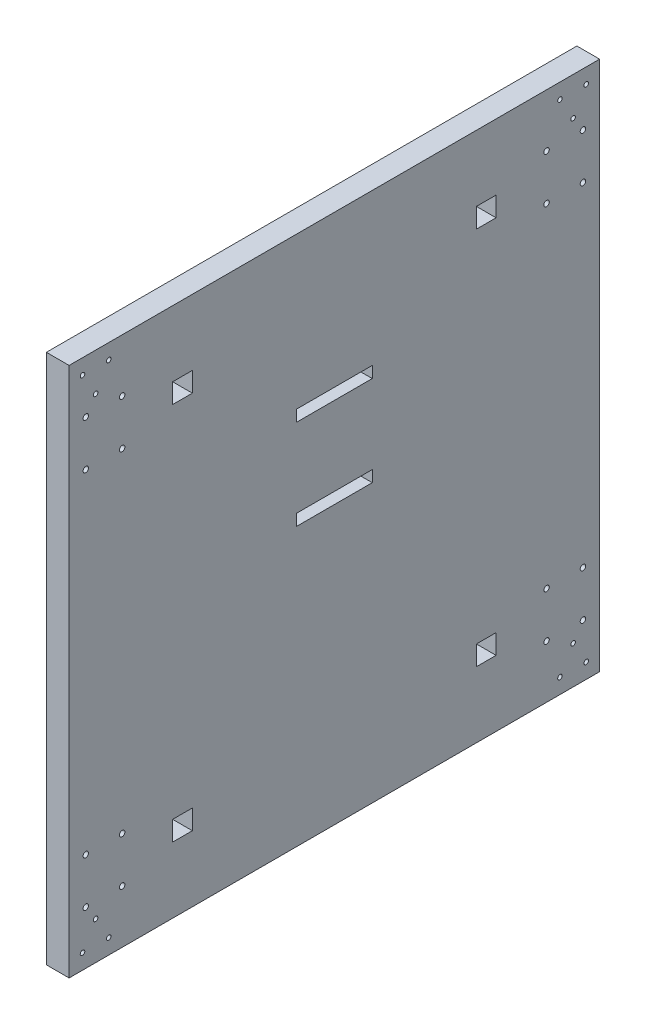
SolidWorks part; units mm, degrees
ref_plane "Front Plane" through (0, 0, 0) normal (0, 0, 1) x (1, 0, 0)
ref_plane "Top Plane" through (0, 0, 0) normal (0, 1, 0) x (1, 0, 0)
ref_plane "Right Plane" through (0, 0, 0) normal (1, 0, 0) x (0, 0, -1)
sketch "Sketch2" plane through (0, 0, 0) normal (1, 0, 0) x (0, 0, -1)
  line L0 (-336.1732, 61.8255) -> (-336.1732, -288.1745)
  line L1 (-336.1732, 61.8255) -> (13.8268, 61.8255)
  line L3 (-336.1732, -288.1745) -> (13.8268, -288.1745)
  line L4 (13.8268, 61.8255) -> (13.8268, -288.1745)
  line L10 (-161.1732, -38.1745) -> (-136.1732, -38.1745)
  line L11 (-54.4741, 18.3245) -> (-67.472, 18.3245)
  line L12 (-67.472, 5.3266) -> (-67.472, 18.3245)
  line L13 (-267.8723, 5.3266) -> (-254.8744, 5.3266)
  line L14 (-54.4741, 5.3266) -> (-67.472, 5.3266)
  line L15 (-267.8723, 5.3266) -> (-267.8723, 18.3245)
  line L16 (-267.8723, 18.3245) -> (-254.8744, 18.3245)
  line L17 (-254.8744, 5.3266) -> (-254.8744, 18.3245)
  line L18 (-261.3734, 18.3245) -> (-261.3734, 5.3266) construction
  line L19 (-267.8723, 11.8255) -> (-254.8744, 11.8255) construction
  line L20 (-54.4741, 5.3266) -> (-54.4741, 18.3245)
  line L21 (-54.4741, -231.6755) -> (-54.4741, -244.6734)
  line L22 (-54.4741, -231.6755) -> (-67.472, -231.6755)
  line L23 (-67.472, -231.6755) -> (-67.472, -244.6734)
  line L24 (-54.4741, -244.6734) -> (-67.472, -244.6734)
  line L25 (-267.8723, -244.6734) -> (-254.8744, -244.6734)
  line L26 (-254.8744, -231.6755) -> (-254.8744, -244.6734)
  line L27 (-267.8723, -231.6755) -> (-254.8744, -231.6755)
  line L28 (-267.8723, -231.6755) -> (-267.8723, -244.6734)
  line L33 (-161.1732, -38.1745) -> (-186.1732, -38.1745)
  line L34 (-186.1732, -38.1745) -> (-186.1732, -45.6745)
  line L35 (-186.1732, -45.6745) -> (-136.1732, -45.6745)
  line L36 (-136.1732, -45.6745) -> (-136.1732, -38.1745)
  line L39 (-161.1732, -105.1745) -> (-136.1732, -105.1745)
  line L40 (-136.1732, -97.6745) -> (-136.1732, -105.1745)
  line L41 (-186.1732, -97.6745) -> (-136.1732, -97.6745)
  line L42 (-186.1732, -105.1745) -> (-186.1732, -97.6745)
  line L43 (-161.1732, -105.1745) -> (-186.1732, -105.1745)
  circle A0 centre (-301.1732, 26.8255) radius 1.8
  circle A1 centre (-301.1732, -3.1745) radius 1.8
  circle A2 centre (-325.1732, -3.1745) radius 1.8
  circle A3 centre (-325.1732, 26.8255) radius 1.8
  circle A4 centre (-301.1732, -223.1745) radius 1.8
  circle A5 centre (-325.1732, -223.1745) radius 1.8
  circle A6 centre (-301.1732, -253.1745) radius 1.8
  circle A7 centre (-325.1732, -253.1745) radius 1.8
  circle A8 centre (-21.1732, -3.1745) radius 1.8
  circle A9 centre (2.8268, -3.1745) radius 1.8
  circle A10 centre (2.8268, 26.8255) radius 1.8
  circle A11 centre (-21.1732, 26.8255) radius 1.8
  circle A12 centre (2.8268, -223.1745) radius 1.8
  circle A13 centre (-21.1732, -223.1745) radius 1.8
  circle A14 centre (-21.1732, -253.1745) radius 1.8
  circle A15 centre (2.8268, -253.1745) radius 1.8
  circle A17 centre (-3.6732, -263.1745) radius 1.5
  circle A18 centre (4.987, -278.1745) radius 1.5
  circle A19 centre (-12.3335, -278.1745) radius 1.5
  circle A20 centre (-12.3335, 51.8255) radius 1.5
  circle A21 centre (4.987, 51.8255) radius 1.5
  circle A22 centre (-3.6732, 36.8255) radius 1.5
  circle A23 centre (-318.6732, 36.8255) radius 1.5
  circle A24 centre (-327.3335, 51.8255) radius 1.5
  circle A25 centre (-310.013, 51.8255) radius 1.5
  circle A26 centre (-327.3335, -278.1745) radius 1.5
  circle A27 centre (-310.013, -278.1745) radius 1.5
  circle A28 centre (-318.6732, -263.1745) radius 1.5
  dimension "D5" = 30
  dimension "D7" = 3
  dimension "D8" = 3
  dimension "D9" = 3.6
  dimension "D1" = 350
  dimension "D2" = 350
  dimension "D3" = 12.9979
  dimension "D4" = 12.9979
  dimension "D6" = 24
extrude "Boss-Extrude2" add sketch "Sketch2" along normal blind 15
